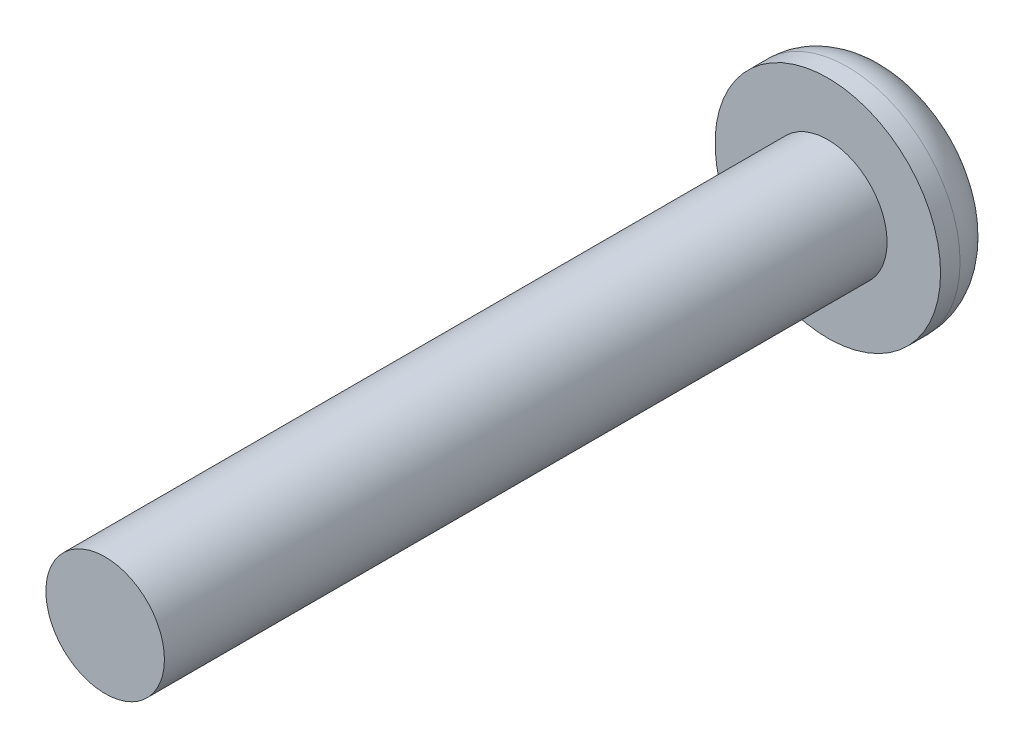
SolidWorks part; units mm, degrees
ref_plane "Front Plane" through (0, 0, 0) normal (0, 0, 1) x (1, 0, 0)
ref_plane "Top Plane" through (0, 0, 0) normal (0, 1, 0) x (1, 0, 0)
ref_plane "Right Plane" through (0, 0, 0) normal (1, 0, 0) x (0, 0, -1)
sketch "Sketch1" plane through (0, 0, 0) normal (0, 0, 1) x (1, 0, 0)
  circle A0 centre (0, 0) radius 3.9624
  dimension "D1" = 7.9248
extrude "Extrude1" add sketch "Sketch1" along normal blind 2.2098
fillet "Fillet1" radius 1.524 1 edges at (3.9624, 0, 0)
sketch "Sketch2" plane through (0, 0, 2.2098) normal (0, 0, 1) x (1, 0, 0)
  circle A0 centre (0, 0) radius 2.0828
  dimension "D1" = 4.1656
extrude "Extrude2" add sketch "Sketch2" along normal blind 25.4
sketch "Sketch3" plane through (0, 0, 0) normal (0, 0, -1) x (-1, 0, 0)
  line L1 (0.709, 1.1779) -> (-0.6656, 1.203)
  line L3 (-0.6656, 1.203) -> (-1.3746, 0.0251)
  line L5 (-1.3746, 0.0251) -> (-0.709, -1.1779)
  line L6 (-0.709, -1.1779) -> (0.6656, -1.203)
  line L7 (0.6656, -1.203) -> (1.3746, -0.0251)
  line L8 (1.3746, -0.0251) -> (0.709, 1.1779)
  circle A1 centre (0, 0) radius 1.1906 construction
  point P0 (0, 0)
  point P8 (0, 0)
  dimension "D1" = 2.3813
extrude "Extrude3" cut sketch "Sketch3" against normal blind 1.016
